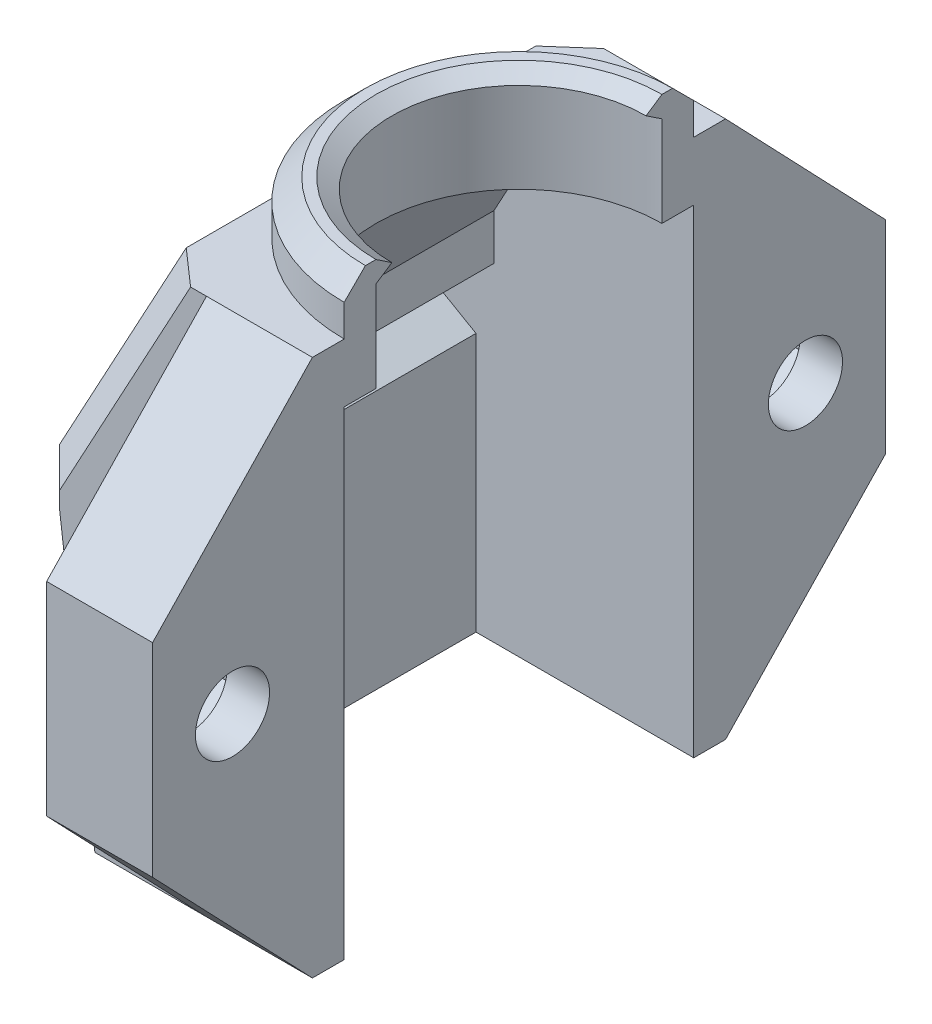
SolidWorks part; units mm, degrees
ref_plane "Front Plane" through (0, 0, 0) normal (0, 0, 1) x (1, 0, 0)
ref_plane "Top Plane" through (0, 0, 0) normal (0, 1, 0) x (1, 0, 0)
ref_plane "Right Plane" through (0, 0, 0) normal (1, 0, 0) x (0, 0, -1)
sketch "Sketch1" plane through (0, 0, 0) normal (0, 0, 1) x (1, 0, 0)
  line L0 (-10.279, -12.6848) -> (-10.279, -0.4735)
  line L1 (-11.9441, 0.4878) -> (-11.9441, 1.6425)
  line L2 (11.779, -12.6848) -> (-11.779, -12.6848)
  line L3 (-9.4275, 2.8152) -> (-9.4275, 4.9732)
  line L4 (-9.913, 2.8152) -> (-9.4275, 2.8152)
  line L5 (-9.913, 2.8152) -> (-11.9441, 1.6425)
  line L6 (-10.279, -0.4735) -> (-11.9441, 0.4878)
  line L7 (-6.75, 9.9108) -> (-9.4275, 4.9732)
  line L8 (9.913, 2.8152) -> (9.4275, 2.8152)
  line L9 (10.279, -12.6848) -> (10.279, -0.4735)
  line L10 (9.913, 2.8152) -> (11.9441, 1.6425)
  line L11 (11.9441, 0.4878) -> (11.9441, 1.6425)
  line L12 (9.4275, 2.8152) -> (9.4275, 4.9732)
  line L13 (10.279, -0.4735) -> (11.9441, 0.4878)
  line L14 (6.75, 9.9108) -> (9.4275, 4.9732)
  line L15 (-6.75, 9.9108) -> (6.75, 9.9108)
  line L16 (0, 12.6848) -> (0, -12.6848) construction
  line L22 (-7.4562, 12.6848) -> (7.4562, 12.6848)
  line L23 (-13.4441, 0.4878) -> (-13.4441, 1.6425)
  line L24 (-11.779, -12.6848) -> (-13.4441, 0.4878)
  line L25 (-7.4562, 12.6848) -> (-13.4441, 1.6425)
  line L26 (13.4441, 0.4878) -> (13.4441, 1.6425)
  line L27 (7.4562, 12.6848) -> (13.4441, 1.6425)
  line L28 (11.779, -12.6848) -> (13.4441, 0.4878)
extrude "Boss-Extrude1" add sketch "Sketch1" along normal blind 19.5 contours L2 L28 L26 L27 L22 L25 L23 L24 L0 L6 L1 L5 L4 L3 L7 L15 L14 L12 L8 L10 L11 L13 L9
sketch "Sketch6" plane through (0, 0, 19.5) normal (0, 0, 1) x (1, 0, 0)
  line L0 (0, 12.6848) -> (-7.4562, 12.6848)
  line L1 (-7.4562, 12.6848) -> (-13.4441, 1.6425)
  line L2 (-13.4441, 1.6425) -> (-13.4441, 0.4878)
  line L3 (-13.4441, 0.4878) -> (-11.779, -12.6848)
  line L4 (-11.779, -12.6848) -> (0, -12.6848)
  line L5 (0, -12.6848) -> (0, 12.6848)
extrude "Boss-Extrude5" add sketch "Sketch6" against normal blind 1.5
sketch "Sketch7" plane through (0, 0, 0) normal (0, 0, -1) x (-1, 0, 0)
  line L0 (0, 12.6848) -> (0, -12.6848)
  line L1 (0, -12.6848) -> (11.779, -12.6848)
  line L2 (11.779, -12.6848) -> (13.4441, 0.4878)
  line L3 (13.4441, 0.4878) -> (13.4441, 1.6425)
  line L4 (13.4441, 1.6425) -> (7.4562, 12.6848)
  line L5 (7.4562, 12.6848) -> (0, 12.6848)
extrude "Boss-Extrude6" add sketch "Sketch7" against normal blind 1.5
sketch "Sketch8" plane through (0, 12.6848, 0) normal (0, 1, 0) x (1, 0, 0)
  line L0 (0, -19.5) -> (0, 0) construction
  circle A0 centre (0, -9.75) radius 6.75
  dimension "D1" = 13.5
extrude "Cut-Extrude2" cut sketch "Sketch8" against normal through all
sketch "Sketch9" plane through (0, 12.6848, 0) normal (0, 1, 0) x (1, 0, 0)
  line L0 (0, -1.5) -> (0, -3)
  line L1 (0, -16.5) -> (0, -18)
  arc A0 (0, -3) -> (0, -16.5) centre (0, -9.75) ccw
  arc A1 (0, -1.5) -> (0, -18) centre (0, -9.75) ccw
  circle A3 centre (0, -9.75) radius 6.75 construction
  circle A4 centre (0, -9.75) radius 8.25 construction
  point P1 (8.25, -9.75)
  point P12 (6.4551, -7.7765)
  dimension "D1" = 1.5
extrude "Boss-Extrude7" add sketch "Sketch9" along normal mid plane 5
sketch "Sketch10" plane through (0, 0, 0) normal (1, 0, 0) x (0, 0, -1)
  line L0 (-19.5, 12.6848) -> (-27.0438, 4.7969)
  line L1 (-20.3969, 1.6599) -> (-23.2719, 3.3198)
  line L2 (-23.2719, 3.3198) -> (-26.1469, 1.6599)
  line L3 (-26.1469, 1.6599) -> (-26.1469, -1.6599)
  line L4 (-26.1469, -1.6599) -> (-23.2719, -3.3198)
  line L5 (-23.2719, -3.3198) -> (-20.3969, -1.6599)
  line L6 (-20.3969, -1.6599) -> (-20.3969, 1.6599)
  line L7 (-9.75, 15.1848) -> (-9.75, -12.6848) construction
  line L8 (-27.0438, -4.7969) -> (-19.5, -12.6848)
  line L9 (-27.0438, 0) -> (-19.5, 0) construction
  line L10 (-19.5, 12.6848) -> (-19.5, -12.6848)
  line L11 (-27.0438, 4.7969) -> (-27.0438, -4.7969)
  line L12 (-3, 15.1848) -> (-16.5, 15.1848) construction
  line L13 (-18, -12.6848) -> (-1.5, -12.6848) construction
  line L14 (-27.0438, 4.7969) -> (-19.5, 12.6848)
  line L15 (-23.2719, 3.3198) -> (-20.3969, 1.6599)
  line L16 (-26.1469, 1.6599) -> (-23.2719, 3.3198)
  line L17 (-23.2719, -3.3198) -> (-26.1469, -1.6599)
  line L18 (-20.3969, -1.6599) -> (-23.2719, -3.3198)
  line L19 (-19.5, -12.6848) -> (-27.0438, -4.7969)
  line L20 (7.5438, 0) -> (0, 0) construction
  line L21 (0, -12.6848) -> (7.5438, -4.7969)
  line L22 (0.8969, -1.6599) -> (3.7719, -3.3198)
  line L23 (3.7719, -3.3198) -> (6.6469, -1.6599)
  line L24 (6.6469, 1.6599) -> (3.7719, 3.3198)
  line L25 (3.7719, 3.3198) -> (0.8969, 1.6599)
  line L26 (7.5438, 4.7969) -> (0, 12.6848)
  line L27 (7.5438, 4.7969) -> (7.5438, -4.7969)
  line L28 (0, 12.6848) -> (0, -12.6848)
  line L29 (7.5438, -4.7969) -> (0, -12.6848)
  line L30 (0.8969, -1.6599) -> (0.8969, 1.6599)
  line L31 (3.7719, -3.3198) -> (0.8969, -1.6599)
  line L32 (6.6469, -1.6599) -> (3.7719, -3.3198)
  line L33 (6.6469, 1.6599) -> (6.6469, -1.6599)
  line L34 (3.7719, 3.3198) -> (6.6469, 1.6599)
  line L35 (0.8969, 1.6599) -> (3.7719, 3.3198)
  line L36 (0, 12.6848) -> (7.5438, 4.7969)
  circle A0 centre (-23.2719, 0) radius 1.75
  circle A1 centre (-23.2719, 0) radius 2.875 construction
  circle A2 centre (3.7719, 0) radius 2.875 construction
  circle A3 centre (3.7719, 0) radius 1.75
  line M3 (-19.5, 12.6848) -> (-19.5, -12.6848)
  dimension "D1" = 3.5
  dimension "D2" = 5.75
extrude "Boss-Extrude8" add sketch "Sketch10" against normal blind 5 contours L0 L11 L8 L6 L5 L4 L3 L2 L1 M3 | L5 L6 L1 L2 L3 L4 A0 | L33 L24 L25 L30 L22 L23 A3 | L26 L28 L21 L27 L24 L33 L23 L22 L30 L25
chamfer "Chamfer1" distance 1.5 angle 45 6 edges at (-12.6115, -6.0985, 19.5) (-13.4441, 1.0652, 19.5) (-10.4501, 7.1637, 19.5) (-12.6115, -6.0985, 0) (-13.4441, 1.0652, 0) (-10.4501, 7.1637, 0)
sketch "Sketch11" plane through (-5, 0, 0) normal (-1, 0, 0) x (0, 0, 1)
  line L0 (23.2719, -3.3198) -> (20.3969, -1.6599) construction
  line L1 (20.3969, -1.6599) -> (20.3969, 1.6599) construction
  line L2 (20.3969, -1.6599) -> (23.2719, -3.3198) construction
  line L3 (26.1469, -1.6599) -> (23.2719, -3.3198) construction
  line L4 (23.2719, -3.3198) -> (26.1469, -1.6599) construction
  line L5 (26.1469, 1.6599) -> (26.1469, -1.6599) construction
  line L6 (23.2719, 3.3198) -> (26.1469, 1.6599) construction
  line L7 (26.1469, 1.6599) -> (23.2719, 3.3198) construction
  line L8 (20.3969, 1.6599) -> (23.2719, 3.3198) construction
  line L9 (23.2719, 3.3198) -> (20.3969, 1.6599) construction
  line L10 (19.5, 12.6848) -> (27.0438, 4.7969) construction
  line L11 (27.0438, 4.7969) -> (27.0438, -4.7969) construction
  line L12 (27.0438, 4.7969) -> (19.5, 12.6848) construction
  line L13 (19.5, 12.6848) -> (19.5, -12.6848) construction
  line L14 (-3.7719, -3.3198) -> (-6.6469, -1.6599) construction
  line L15 (-6.6469, -1.6599) -> (-3.7719, -3.3198) construction
  line L16 (-6.6469, 1.6599) -> (-6.6469, -1.6599) construction
  line L17 (-0.8969, -1.6599) -> (-3.7719, -3.3198) construction
  line L18 (-3.7719, -3.3198) -> (-0.8969, -1.6599) construction
  line L19 (-0.8969, -1.6599) -> (-0.8969, 1.6599) construction
  line L20 (0, -12.6848) -> (-7.5438, -4.7969) construction
  line L21 (-7.5438, 4.7969) -> (-7.5438, -4.7969) construction
  line L22 (-7.5438, -4.7969) -> (0, -12.6848) construction
  line L23 (0, 12.6848) -> (0, -12.6848) construction
  line L24 (27.0438, -4.7969) -> (19.5, -12.6848) construction
  line L25 (19.5, -12.6848) -> (27.0438, -4.7969) construction
  line L26 (-7.5438, 4.7969) -> (0, 12.6848) construction
  line L27 (0, 12.6848) -> (-7.5438, 4.7969) construction
  line L28 (-3.7719, 3.3198) -> (-0.8969, 1.6599) construction
  line L29 (-0.8969, 1.6599) -> (-3.7719, 3.3198) construction
  line L30 (-6.6469, 1.6599) -> (-3.7719, 3.3198) construction
  line L31 (-3.7719, 3.3198) -> (-6.6469, 1.6599) construction
  line L32 (23.2719, -3.3198) -> (20.3969, -1.6599)
  line L33 (20.3969, -1.6599) -> (20.3969, 1.6599)
  line L34 (20.3969, -1.6599) -> (23.2719, -3.3198)
  line L35 (26.1469, -1.6599) -> (23.2719, -3.3198)
  line L36 (23.2719, -3.3198) -> (26.1469, -1.6599)
  line L37 (26.1469, 1.6599) -> (26.1469, -1.6599)
  line L38 (23.2719, 3.3198) -> (26.1469, 1.6599)
  line L39 (26.1469, 1.6599) -> (23.2719, 3.3198)
  line L40 (20.3969, 1.6599) -> (23.2719, 3.3198)
  line L41 (23.2719, 3.3198) -> (20.3969, 1.6599)
  line L42 (19.5, 12.6848) -> (27.0438, 4.7969)
  line L43 (27.0438, 4.7969) -> (27.0438, -4.7969)
  line L44 (27.0438, 4.7969) -> (19.5, 12.6848)
  line L45 (19.5, 12.6848) -> (19.5, -12.6848)
  line L46 (-3.7719, -3.3198) -> (-6.6469, -1.6599)
  line L47 (-6.6469, -1.6599) -> (-3.7719, -3.3198)
  line L48 (-6.6469, 1.6599) -> (-6.6469, -1.6599)
  line L49 (-0.8969, -1.6599) -> (-3.7719, -3.3198)
  line L50 (-3.7719, -3.3198) -> (-0.8969, -1.6599)
  line L51 (-0.8969, -1.6599) -> (-0.8969, 1.6599)
  line L52 (0, -12.6848) -> (-7.5438, -4.7969)
  line L53 (-7.5438, 4.7969) -> (-7.5438, -4.7969)
  line L54 (-7.5438, -4.7969) -> (0, -12.6848)
  line L55 (0, 12.6848) -> (0, -12.6848)
  line L56 (27.0438, -4.7969) -> (19.5, -12.6848)
  line L57 (19.5, -12.6848) -> (27.0438, -4.7969)
  line L58 (-7.5438, 4.7969) -> (0, 12.6848)
  line L59 (0, 12.6848) -> (-7.5438, 4.7969)
  line L60 (-3.7719, 3.3198) -> (-0.8969, 1.6599)
  line L61 (-0.8969, 1.6599) -> (-3.7719, 3.3198)
  line L62 (-6.6469, 1.6599) -> (-3.7719, 3.3198)
  line L63 (-3.7719, 3.3198) -> (-6.6469, 1.6599)
  circle A0 centre (23.2719, 0) radius 1.75 construction
  circle A1 centre (-3.7719, 0) radius 1.75 construction
  circle A2 centre (23.2719, 0) radius 1.75
  circle A3 centre (-3.7719, 0) radius 1.75
  circle M1 centre (-3.7719, 0) radius 1.75
extrude "Cut-Extrude3" cut sketch "Sketch11" against normal blind 3 contours L62 L48 L46 L49 L51 L60 M1 | L40 L33 L32 L35 L37 L38 A2
chamfer "Chamfer2" distance 1 angle 45 1 edges at (-8.25, 15.1848, 9.75)
sketch "Sketch12" plane through (0, 0, 0) normal (1, 0, 0) x (0, 0, -1)
  line L0 (-16.5, 15.1848) -> (-16.5, 14.1848)
  line L1 (-16.5, 15.1848) -> (-16.5, 9.9108) construction
  line L2 (-16.5, 14.6848) -> (-15.75, 14.6848) construction
  line L3 (-16.5, 15.1848) -> (-15.75, 14.6848)
  line L4 (-15.75, 14.6848) -> (-16.5, 14.1848)
  line L5 (-9.75, 15.1848) -> (-9.75, -12.6848) construction
  line L6 (-3, 15.1848) -> (-16.5, 15.1848) construction
  line L7 (-18, -12.6848) -> (-1.5, -12.6848) construction
revolve "Revolve1" add sketch "Sketch12" angle 180 about L5
